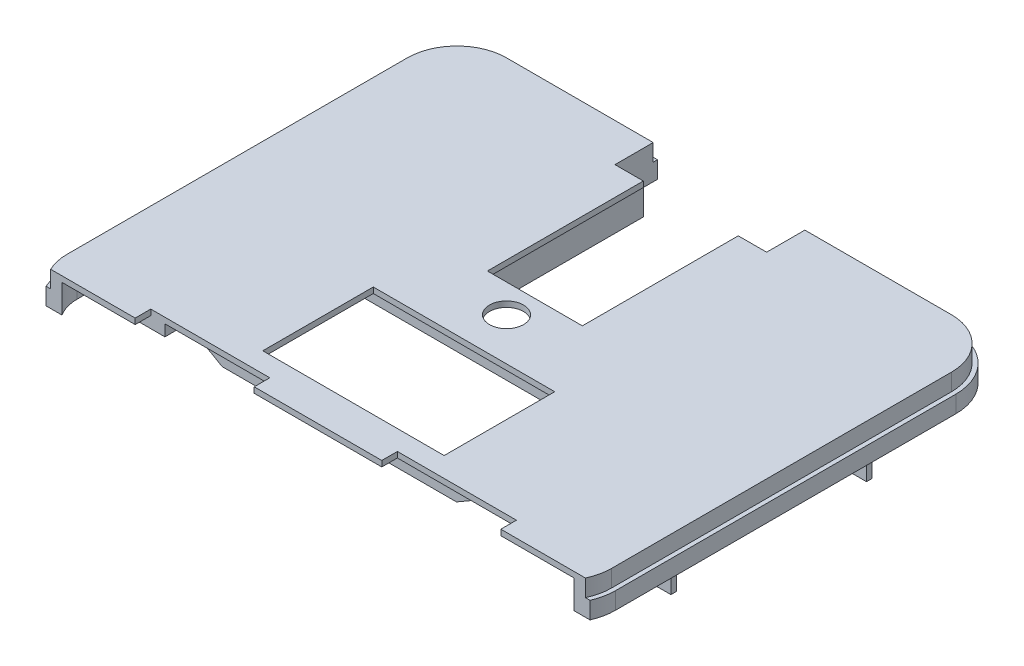
SolidWorks part; units mm, degrees
ref_plane "Front Plane" through (0, 0, 0) normal (0, 0, 1) x (1, 0, 0)
ref_plane "Top Plane" through (0, 0, 0) normal (0, 1, 0) x (1, 0, 0)
ref_plane "Right Plane" through (0, 0, 0) normal (1, 0, 0) x (0, 0, -1)
sketch "Sketch1" plane through (0, 0, 0) normal (0, 1, 0) x (1, 0, 0)
  line L0 (124.25, 158) -> (176, 158)
  line L1 (19, 0) -> (33, 0)
  line L2 (0, 19) -> (0, 139)
  line L3 (19, 158) -> (70.75, 158)
  line L4 (195, 19) -> (195, 139)
  line L5 (33, 0) -> (33, 17)
  line L6 (80.75, 143) -> (80.75, 88)
  line L7 (80.75, 88) -> (114.25, 88)
  line L8 (114.25, 143) -> (114.25, 88)
  line L9 (33, 17) -> (75, 17)
  line L10 (75, 17) -> (75, 0)
  line L11 (97.5, 0) -> (97.5, 17) construction
  line L12 (120, 17) -> (120, 0)
  line L13 (162, 17) -> (120, 17)
  line L14 (162, 0) -> (162, 17)
  line L15 (162, 0) -> (176, 0)
  line L16 (75, 0) -> (120, 0)
  line L17 (80.75, 143) -> (70.75, 143)
  line L18 (70.75, 143) -> (70.75, 158)
  line L19 (19, 158) -> (176, 158) construction
  line L20 (124.25, 158) -> (124.25, 143)
  line L21 (124.25, 143) -> (114.25, 143)
  line L23 (122.5, -1) -> (72.5, -1) construction
  arc A0 (176, 0) -> (195, 19) centre (176, 19) ccw
  arc A1 (0, 139) -> (19, 158) centre (19, 139) cw
  arc A2 (176, 158) -> (195, 139) centre (176, 139) cw
  arc A3 (19, 0) -> (0, 19) centre (19, 19) cw
  point P9 (0, 158)
  point P12 (195, 158)
  point P15 (0, 0)
  point P32 (97.5, 88)
  point P36 (97.5, 158)
  point P43 (97.5, -1)
  dimension "D3" = 19
  dimension "D1" = 158
  dimension "D2" = 195
  dimension "D4" = 55
  dimension "D5" = 33.5
  dimension "D6" = 33
  dimension "D7" = 42
  dimension "D8" = 17
  dimension "D9" = 15
  dimension "D10" = 10
extrude "Boss-Extrude1" add sketch "Sketch1" along normal blind 2
sketch "Sketch2" plane through (0, 0, 0) normal (0, -1, 0) x (1, 0, 0)
  line L0 (0, -139) -> (0, -19) construction
  line L1 (75, 0) -> (75, -5)
  line L2 (33, 0) -> (33, -5)
  line L3 (120, 0) -> (120, -5)
  line L5 (97.5, 0) -> (97.5, -88) construction
  line L6 (75, 0) -> (120, 0) construction
  line L7 (114.25, -88) -> (80.75, -88) construction
  line L11 (162, 0) -> (162, -5)
  line L14 (124.25, -153) -> (124.25, -158)
  line L16 (70.75, -153) -> (70.75, -158)
  line L25 (162, 0) -> (176, 0) construction
  line L26 (195, -19) -> (195, -139) construction
  line L27 (176, -158) -> (124.25, -158) construction
  line L28 (70.75, -158) -> (19, -158) construction
  line L29 (19, 0) -> (33, 0) construction
  line L30 (75, 0) -> (120, 0)
  line L31 (162, 0) -> (176, 0)
  line L32 (195, -19) -> (195, -139)
  line L33 (176, -158) -> (124.25, -158)
  line L34 (70.75, -158) -> (19, -158)
  line L35 (0, -139) -> (0, -19)
  line L36 (19, 0) -> (33, 0)
  line L37 (33, 0) -> (75, 0) construction
  line L38 (120, 0) -> (162, 0) construction
  line L39 (70.75, -158) -> (124.25, -158) construction
  line L40 (70.75, -153) -> (19, -153)
  line L41 (5, -139) -> (5, -19)
  line L42 (19, -5) -> (33, -5)
  line L43 (75, -5) -> (120, -5)
  line L44 (162, -5) -> (176, -5)
  line L45 (190, -19) -> (190, -139)
  line L46 (176, -153) -> (124.25, -153)
  arc A0 (195, -19) -> (176, 0) centre (176, -19) ccw construction
  arc A1 (176, -158) -> (195, -139) centre (176, -139) ccw construction
  arc A2 (0, -139) -> (19, -158) centre (19, -139) ccw construction
  arc A3 (19, 0) -> (0, -19) centre (19, -19) ccw construction
  arc A4 (195, -19) -> (176, 0) centre (176, -19) ccw
  arc A5 (176, -158) -> (195, -139) centre (176, -139) ccw
  arc A6 (0, -139) -> (19, -158) centre (19, -139) ccw
  arc A7 (19, 0) -> (0, -19) centre (19, -19) ccw
  arc A8 (5, -139) -> (19, -153) centre (19, -139) ccw
  arc A9 (19, -5) -> (5, -19) centre (19, -19) ccw
  arc A10 (190, -19) -> (176, -5) centre (176, -19) ccw
  arc A11 (176, -153) -> (190, -139) centre (176, -139) ccw
  dimension "D7" = 5
extrude "Boss-Extrude2" add sketch "Sketch2" along normal blind 10
sketch "Sketch3" plane through (0, 0, 0) normal (0, -1, 0) x (1, 0, 0)
  line L2 (190, -43.5) -> (150, -43.5)
  line L3 (190, -45.5) -> (152, -45.5)
  line L4 (190, -114.5) -> (150, -114.5)
  line L6 (150, -43.5) -> (150, -114.5)
  line L7 (152, -45.5) -> (152, -112.5)
  line L8 (190, -112.5) -> (152, -112.5)
  line L9 (187.7731, -112.5) -> (152, -112.5) construction
  line L10 (187.7731, -114.5) -> (150, -114.5) construction
  line L11 (190, -112.5) -> (190, -114.5)
  line L12 (190, -43.5) -> (190, -45.5)
  line L13 (190, -19) -> (190, -139) construction
  point P6 (150, -79)
  point P7 (190, -79)
  dimension "D1" = 40
  dimension "D2" = 71
  dimension "D3" = 2
extrude "Boss-Extrude3" add sketch "Sketch3" along normal blind 20
sketch "Sketch4" plane through (152, 0, 0) normal (1, 0, 0) x (0, 0, -1)
  line L0 (112.5, -20) -> (112.5, 0) construction
  line L1 (45.5, -20) -> (112.5, -20)
  line L2 (45.5, -20) -> (45.5, -18)
  line L3 (45.5, -18) -> (112.5, -18)
  line L4 (112.5, -20) -> (112.5, -18)
  dimension "D1" = 2
extrude "Boss-Extrude4" add sketch "Sketch4" along normal blind 5
sketch "Sketch5" plane through (0, 0, 0) normal (0, -1, 0) x (1, 0, 0)
  line L0 (70.75, -153) -> (70.75, -80.7) construction
  line L1 (14.25, -151.5) -> (14.25, -82.2)
  line L2 (14.25, -151.5) -> (69.25, -151.5)
  line L3 (69.25, -151.5) -> (69.25, -82.2)
  line L4 (14.25, -82.2) -> (69.25, -82.2)
  line L5 (70.75, -80.7) -> (70.75, -153)
  line L6 (12.75, -153) -> (70.75, -153)
  line L7 (69.25, -151.5) -> (14.25, -82.2) construction
  line L8 (12.75, -80.7) -> (70.75, -80.7)
  line L9 (12.75, -153) -> (12.75, -80.7)
  line L10 (69.25, -82.2) -> (14.25, -151.5) construction
  line L11 (70.75, -153) -> (19, -153) construction
  line L13 (70.75, -143) -> (70.75, -153) construction
  dimension "D1" = 69.3
  dimension "D2" = 55
  dimension "D4" = 0
  dimension "D3" = 1.5
extrude "Boss-Extrude5" add sketch "Sketch5" along normal blind 19
sketch "Sketch6" plane through (0, 0, -80.7) normal (0, 0, 1) x (1, 0, 0)
  line L1 (15.75, -16) -> (25.75, -16)
  line L2 (15.75, -16) -> (15.75, -3)
  line L3 (15.75, -3) -> (25.75, -3)
  line L4 (70.75, 0) -> (12.75, 0)
  line L5 (12.75, 0) -> (12.75, -19)
  line L6 (12.75, -19) -> (70.75, -19)
  line L7 (70.75, -19) -> (70.75, 0)
  line L8 (70.75, 0) -> (12.75, 0)
  line L9 (12.75, 0) -> (12.75, -19)
  line L10 (12.75, -19) -> (70.75, -19)
  line L11 (70.75, -19) -> (70.75, 0)
  line L12 (25.75, -16) -> (25.75, -3)
  line L13 (58.75, -3) -> (45.75, -3)
  line L14 (58.75, -3) -> (58.75, -16)
  line L15 (58.75, -16) -> (45.75, -16)
  line L16 (45.75, -3) -> (45.75, -16)
  dimension "D2" = 13
  dimension "D3" = 13
  dimension "D4" = 13
  dimension "D5" = 12
  dimension "D6" = 3
  dimension "D7" = 10
  dimension "D8" = 3
  dimension "D9" = 3
  dimension "D1" = 0
extrude "Cut-Extrude1" cut sketch "Sketch6" against normal up to surface (1.5 mm away) contours L13 L16 L15 L14 | L1 L12 L3 L2 up to face at (41.75, -9.5, -82.2)
ref_plane "Plane1" through (29.25, 0, 0) normal (1, 0, 0) x (0, 0, -1)
sketch "Sketch8" plane through (29.25, 0, 0) normal (1, 0, 0) x (0, 0, -1)
  line L0 (151.5, -3.5) -> (150.5, -3.5)
  line L1 (151.5, -19) -> (151.5, 0) construction
  line L2 (150.5, -3.5) -> (151.5, -9.5)
  line L3 (151.5, -9.5) -> (151.5, -3.5)
  line L4 (82.2, 0) -> (151.5, 0) construction
  dimension "D1" = 3.5
  dimension "D2" = 1
extrude "Boss-Extrude6" add sketch "Sketch8" along normal mid plane 20
sketch "Sketch9" plane through (0, -10, 0) normal (0, -1, 0) x (1, 0, 0)
  line L0 (33, 0) -> (19, 0) construction
  line L2 (0, -19) -> (0, -139) construction
  line L6 (19, -158) -> (70.75, -158) construction
  line L9 (124.25, -158) -> (176, -158) construction
  line L21 (120, 0) -> (75, 0) construction
  line L22 (176, 0) -> (162, 0) construction
  line L23 (195, -139) -> (195, -19) construction
  line L24 (124.25, -158) -> (176, -158)
  line L25 (19, -158) -> (70.75, -158)
  line L26 (0, -19) -> (0, -139)
  line L27 (33, 0) -> (19, 0)
  line L28 (120, 0) -> (75, 0)
  line L29 (176, 0) -> (162, 0)
  line L30 (195, -139) -> (195, -19)
  line L31 (33, -1.5) -> (19, -1.5)
  line L32 (1.5, -19) -> (1.5, -139)
  line L33 (19, -156.5) -> (70.75, -156.5)
  line L34 (124.25, -156.5) -> (176, -156.5)
  line L35 (193.5, -139) -> (193.5, -19)
  line L36 (176, -1.5) -> (162, -1.5)
  line L37 (120, -1.5) -> (75, -1.5)
  line L38 (162, 0) -> (162, -1.5)
  line L39 (120, 0) -> (120, -1.5)
  line L40 (75, 0) -> (75, -1.5)
  line L41 (75, -1.5) -> (74.7326, -1.014)
  line L42 (33, 0) -> (33, -1.5)
  line L43 (70.75, -156.5) -> (70.75, -158)
  line L44 (124.25, -156.5) -> (124.25, -158)
  line L45 (124.25, -158) -> (123.3442, -158.0889)
  arc A0 (19, 0) -> (0, -19) centre (19, -19) ccw construction
  arc A2 (0, -139) -> (19, -158) centre (19, -139) ccw construction
  arc A12 (195, -19) -> (176, 0) centre (176, -19) ccw construction
  arc A13 (176, -158) -> (195, -139) centre (176, -139) ccw construction
  arc A14 (0, -139) -> (19, -158) centre (19, -139) ccw
  arc A15 (19, 0) -> (0, -19) centre (19, -19) ccw
  arc A16 (195, -19) -> (176, 0) centre (176, -19) ccw
  arc A17 (176, -158) -> (195, -139) centre (176, -139) ccw
  arc A18 (19, -1.5) -> (1.5, -19) centre (19, -19) ccw
  arc A19 (1.5, -139) -> (19, -156.5) centre (19, -139) ccw
  arc A20 (176, -156.5) -> (193.5, -139) centre (176, -139) ccw
  arc A21 (193.5, -19) -> (176, -1.5) centre (176, -19) ccw
  arc M8 (19, 0) -> (0, -19) centre (19, -19) ccw
  line M9 (0, -19) -> (0, -139)
  arc M10 (0, -139) -> (19, -158) centre (19, -139) ccw
  line M11 (19, -158) -> (70.75, -158)
  line M12 (70.75, -158) -> (70.75, -153)
  line M18 (33, -5) -> (33, 0)
  line M19 (33, 0) -> (19, 0)
  dimension "D1" = 1.5
extrude "Cut-Extrude2" cut sketch "Sketch9" against normal through all from offset 6 contours A19 L32 A18 L31 L33 M18 M19 M8 M9 M10 M11 M12 | A21 L35 A20 L34 L44 L24 A17 L30 A16 L29 L38 L36 | L28 L40 L37 L39 offset against normal yes
sketch "Sketch10" plane through (0, 2, 0) normal (0, 1, 0) x (1, 0, 0)
  line L0 (176, 0) -> (19, 0)
  line L1 (1.5429, 11.5) -> (193.4571, 11.5)
  arc A2 (0, 19) -> (19, 0) centre (19, 19) ccw construction
  arc A3 (1.5429, 11.5) -> (19, 0) centre (19, 19) ccw
  arc A4 (176, 0) -> (195, 19) centre (176, 19) ccw construction
  arc A5 (176, 0) -> (193.4571, 11.5) centre (176, 19) ccw
  dimension "D1" = 11.5
extrude "Cut-Extrude3" cut sketch "Sketch10" against normal up to surface (12 mm away) up to face at (176.2606, -10, -79)
sketch "Sketch11" plane through (0, 0, 0) normal (0, -1, 0) x (1, 0, 0)
  line L0 (150, -114.5) -> (190, -114.5) construction
  line L1 (190, -114.5) -> (190, -139) construction
  line L2 (186, -79) -> (133.1255, -79) construction
  line L3 (190, -45.5) -> (190, -112.5) construction
  circle A0 centre (185, -119.5) radius 2.5
  circle A1 centre (185, -135.5) radius 2.5
  circle A2 centre (185, -119.5) radius 1.5
  circle A3 centre (185, -135.5) radius 1.5
  circle A4 centre (185, -38.5) radius 2.5
  circle A5 centre (185, -22.5) radius 1.5
  circle A6 centre (185, -38.5) radius 1.5
  circle A7 centre (185, -22.5) radius 2.5
  point P14 (190, -79)
  dimension "D1" = 5
  dimension "D2" = 5
  dimension "D4" = 3
  dimension "D5" = 3
  dimension "D3" = 16
  dimension "D6" = 5
  dimension "D7" = 5
extrude "Boss-Extrude7" add sketch "Sketch11" along normal blind 4
sketch "Sketch12" plane through (0, 0, 0) normal (0, -1, 0) x (1, 0, 0)
  line L0 (5, -139) -> (5, -19) construction
  line L1 (5, -18) -> (37, -18)
  line L2 (5, -18) -> (5, -79)
  line L3 (5, -79) -> (37, -79)
  line L4 (37, -18) -> (37, -79)
  line L5 (4, -17) -> (38, -17)
  line L6 (38, -17) -> (38, -80)
  line L7 (4, -80) -> (38, -80)
  line L8 (4, -17) -> (4, -80)
  line L9 (33, -17) -> (75, -17) construction
  dimension "D1" = 32
  dimension "D2" = 61
  dimension "D3" = 1
extrude "Boss-Extrude8" add sketch "Sketch12" along normal blind 4
sketch "Sketch13" plane through (5, 0, 0) normal (1, 0, 0) x (0, 0, -1)
  line L1 (71, -2) -> (63, -2)
  line L2 (71, -2) -> (71, -6)
  line L3 (71, -6) -> (63, -6)
  line L4 (63, -2) -> (63, -6)
  line L5 (79, -4) -> (79, 0) construction
  line L6 (79, 0) -> (19, 0) construction
  dimension "D1" = 8
  dimension "D2" = 8
  dimension "D3" = 4
  dimension "D4" = 2
extrude "Cut-Extrude4" cut sketch "Sketch13" against normal blind 18
sketch "Sketch14" plane through (0, 0, 0) normal (0, -1, 0) x (1, 0, 0)
  line L1 (65.5, -24) -> (129.5, -24)
  line L2 (65.5, -24) -> (65.5, -63)
  line L3 (65.5, -63) -> (129.5, -63)
  line L4 (129.5, -24) -> (129.5, -63)
  line L5 (120, -11.5) -> (75, -11.5) construction
  line L6 (114.25, -88) -> (80.75, -88) construction
  circle A0 centre (97.5, -78) radius 6
  point P6 (97.5, -11.5)
  point P7 (97.5, -24)
  point P13 (97.5, -88)
  dimension "D4" = 12
  dimension "D1" = 64
  dimension "D2" = 39
  dimension "D3" = 25
  dimension "D5" = 10
extrude "Cut-Extrude5" cut sketch "Sketch14" against normal through all both and the other way through all
sketch "Sketch15" plane through (0, 0, 0) normal (0, -1, 0) x (1, 0, 0)
  line L0 (150, -43.5) -> (150, -114.5) construction
  line L1 (47.5, -19) -> (147.5, -19)
  line L2 (47.5, -19) -> (47.5, -22)
  line L3 (47.5, -22) -> (147.5, -22)
  line L4 (147.5, -19) -> (147.5, -22)
  line L5 (38, -65) -> (150, -65)
  line L6 (38, -65) -> (38, -68)
  line L7 (38, -68) -> (150, -68)
  line L8 (150, -65) -> (150, -68)
  line L9 (38, -80) -> (38, -17) construction
  line L10 (120, -11.5) -> (75, -11.5) construction
  line L11 (65.5, -24) -> (129.5, -24) construction
  line L12 (129.5, -63) -> (65.5, -63) construction
  point P10 (0, 0)
  point P11 (0, 0)
  point P14 (97.5, -19)
  point P17 (97.5, -11.5)
  dimension "D1" = 3
  dimension "D2" = 100
  dimension "D3" = 2
  dimension "D4" = 2
extrude "Boss-Extrude9" add sketch "Sketch15" along normal blind 5
sketch "Sketch16" plane through (0, 0, -22) normal (0, 0, -1) x (-1, 0, 0)
  line L4 (-47.5, 0) -> (-56.1603, -5)
  line L5 (-147.5, 0) -> (-138.8397, -5)
  line L6 (-56.1603, -5) -> (-47.5, -5)
  line L8 (-47.5, 0) -> (-147.5, 0)
  line L9 (-147.5, 0) -> (-147.5, -5)
  line L10 (-147.5, -5) -> (-47.5, -5)
  line L11 (-47.5, -5) -> (-47.5, 0)
  line L13 (-147.5, 0) -> (-147.5, -5)
  line L14 (-147.5, -5) -> (-138.8397, -5)
  line L15 (-47.5, -5) -> (-47.5, 0)
  dimension "D2" = 60
  dimension "D1" = 0
extrude "Cut-Extrude6" cut sketch "Sketch16" against normal blind 5
